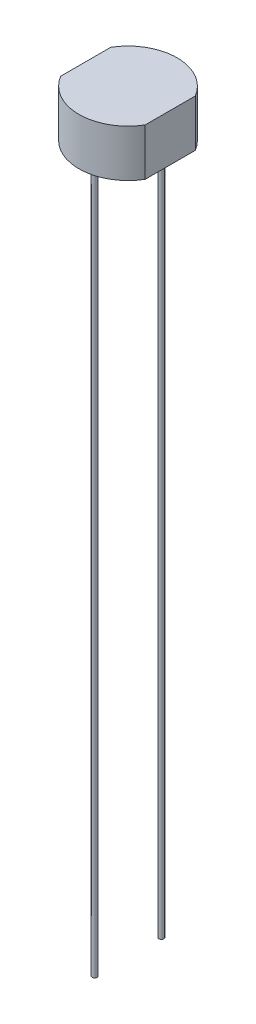
SolidWorks part; units mm, degrees
ref_plane "Front Plane" through (0, 0, 0) normal (0, 0, 1) x (1, 0, 0)
ref_plane "Top Plane" through (0, 0, 0) normal (0, 1, 0) x (1, 0, 0)
ref_plane "Right Plane" through (0, 0, 0) normal (1, 0, 0) x (0, 0, -1)
sketch "Sketch1" plane through (0, 0, 0) normal (0, 1, 0) x (1, 0, 0)
  line L0 (-2.15, 1.2757) -> (-2.15, -1.2757)
  line L1 (2.15, 1.2757) -> (2.15, -1.2757)
  line L2 (-2.15, 0) -> (2.15, 0) construction
  arc A1 (-2.15, 1.2757) -> (2.15, 1.2757) centre (0, 0) cw
  arc A2 (-2.15, -1.2757) -> (2.15, -1.2757) centre (0, 0) ccw
  dimension "D1" = 2.5
  dimension "D2" = 4.3
extrude "Boss-Extrude1" add sketch "Sketch1" along normal blind 2.4 contours A1 L1 A2 L0
sketch "Sketch2" plane through (0, 0, 0) normal (0, 1, 0) x (1, 0, 0)
  line L0 (-2.15, 0) -> (2.15, 0) construction
  line L1 (-2.15, 1.2757) -> (-2.15, -1.2757) construction
  line L2 (2.15, 1.2757) -> (2.15, -1.2757) construction
  circle A0 centre (0, 1.7) radius 0.125
  circle A1 centre (0, -1.7) radius 0.125
  dimension "D1" = 0.25
  dimension "D2" = 1.7
extrude "Boss-Extrude2" add sketch "Sketch2" against normal blind 36
